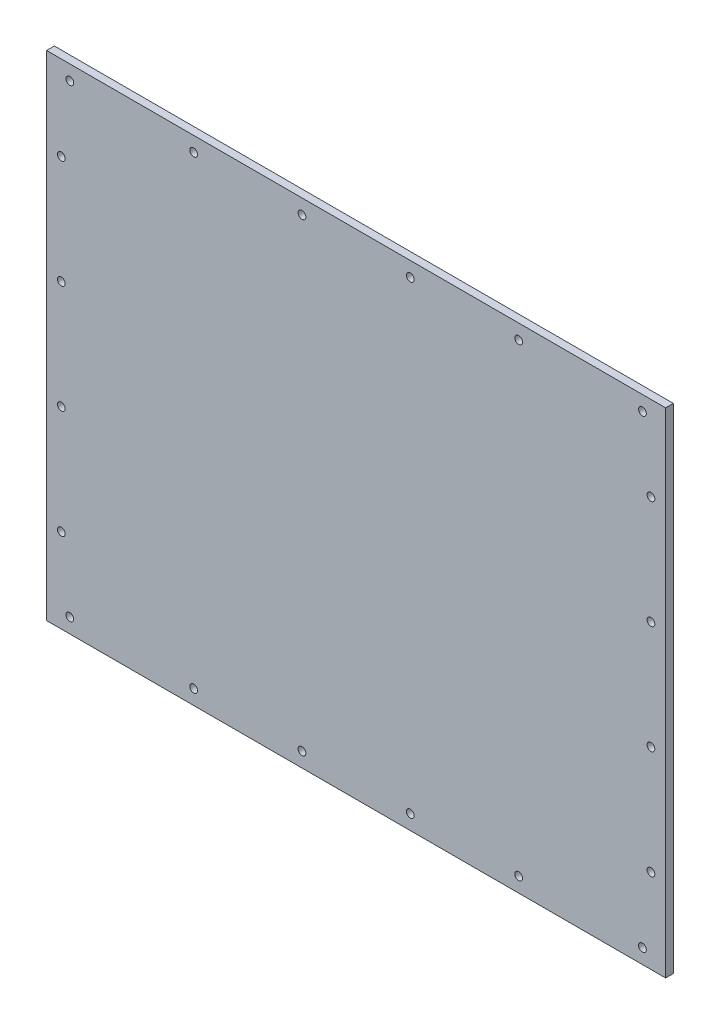
SolidWorks part; units mm, degrees
material "6061 Alloy"
ref_plane "Front Plane" through (0, 0, 0) normal (0, 0, 1) x (1, 0, 0)
ref_plane "Top Plane" through (0, 0, 0) normal (0, 1, 0) x (1, 0, 0)
ref_plane "Right Plane" through (0, 0, 0) normal (1, 0, 0) x (0, 0, -1)
sketch "Sketch1" plane through (0, 0, 0) normal (0, 0, 1) x (1, 0, 0)
  line L1 (0, 0) -> (400, 0)
  line L2 (0, 0) -> (0, 319.05)
  line L3 (0, 319.05) -> (400, 319.05)
  line L4 (400, 0) -> (400, 319.05)
  dimension "D1" = 400
  dimension "D2" = 319.05
extrude "Boss-Extrude1" add sketch "Sketch1" along normal blind 5
sketch "Sketch2" plane through (0, 0, 5) normal (0, 0, 1) x (1, 0, 0)
  line L0 (0, 0) -> (400, 0) construction
  line L1 (0, 159.525) -> (54.0264, 159.525) construction
  line L2 (200, 0) -> (200, 30.7796) construction
  line L3 (0, 319.05) -> (0, 0) construction
  circle A0 centre (15, 9.5) radius 2.5
  circle A1 centre (95, 9.5) radius 2.5
  circle A2 centre (165, 9.5) radius 2.5
  circle A3 centre (235, 9.5) radius 2.5
  circle A4 centre (305, 9.5) radius 2.5
  circle A5 centre (385, 9.5) radius 2.5
  circle A6 centre (385, 309.55) radius 2.5
  circle A7 centre (305, 309.55) radius 2.5
  circle A8 centre (235, 309.55) radius 2.5
  circle A9 centre (165, 309.55) radius 2.5
  circle A10 centre (95, 309.55) radius 2.5
  circle A11 centre (15, 309.55) radius 2.5
  dimension "D1" = 5
  dimension "D4" = 70
  dimension "D5" = 80
  dimension "D3" = 35
  dimension "D2" = 9.5
extrude "Cut-Extrude1" cut sketch "Sketch2" against normal blind 10
sketch "Sketch3" plane through (0, 0, 5) normal (0, 0, 1) x (1, 0, 0)
  line L0 (0, 319.05) -> (0, 0) construction
  line L1 (0, 159.525) -> (51.6751, 159.525) construction
  line L2 (200, 319.05) -> (200, 246.0439) construction
  line L3 (400, 319.05) -> (0, 319.05) construction
  circle A0 centre (9.5, 264.525) radius 2.5
  circle A1 centre (9.5, 194.525) radius 2.5
  circle A4 centre (9.5, 124.525) radius 2.5
  circle A5 centre (9.5, 54.525) radius 2.5
  circle A6 centre (390.5, 54.525) radius 2.5
  circle A7 centre (390.5, 124.525) radius 2.5
  circle A8 centre (390.5, 194.525) radius 2.5
  circle A9 centre (390.5, 264.525) radius 2.5
  dimension "D1" = 5
  dimension "D2" = 9.5
  dimension "D3" = 35
  dimension "D4" = 70
extrude "Cut-Extrude2" cut sketch "Sketch3" against normal through all
